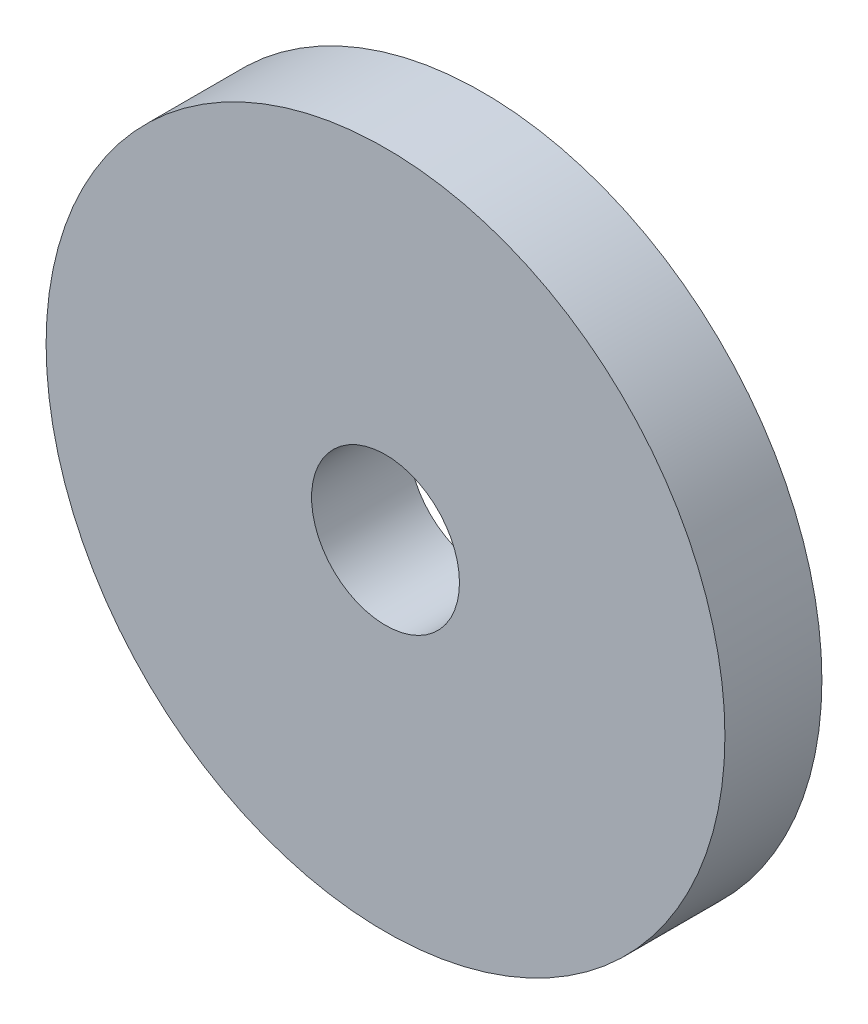
SolidWorks part; units mm, degrees
material "Thornel Mat VMA"
ref_plane "前视基准面" through (0, 0, 0) normal (0, 0, 1) x (1, 0, 0)
ref_plane "上视基准面" through (0, 0, 0) normal (0, 1, 0) x (1, 0, 0)
ref_plane "右视基准面" through (0, 0, 0) normal (1, 0, 0) x (0, 0, -1)
other "Configuration Table"
sketch "草图1" plane through (0, 0, 0) normal (0, 0, 1) x (1, 0, 0)
  circle A0 centre (0, 0) radius 1.525
  circle A1 centre (0, 0) radius 7
  dimension "D1" = 14
  dimension "D2" = 3.05
extrude "凸台-拉伸1" add sketch "草图1" along normal blind 2
